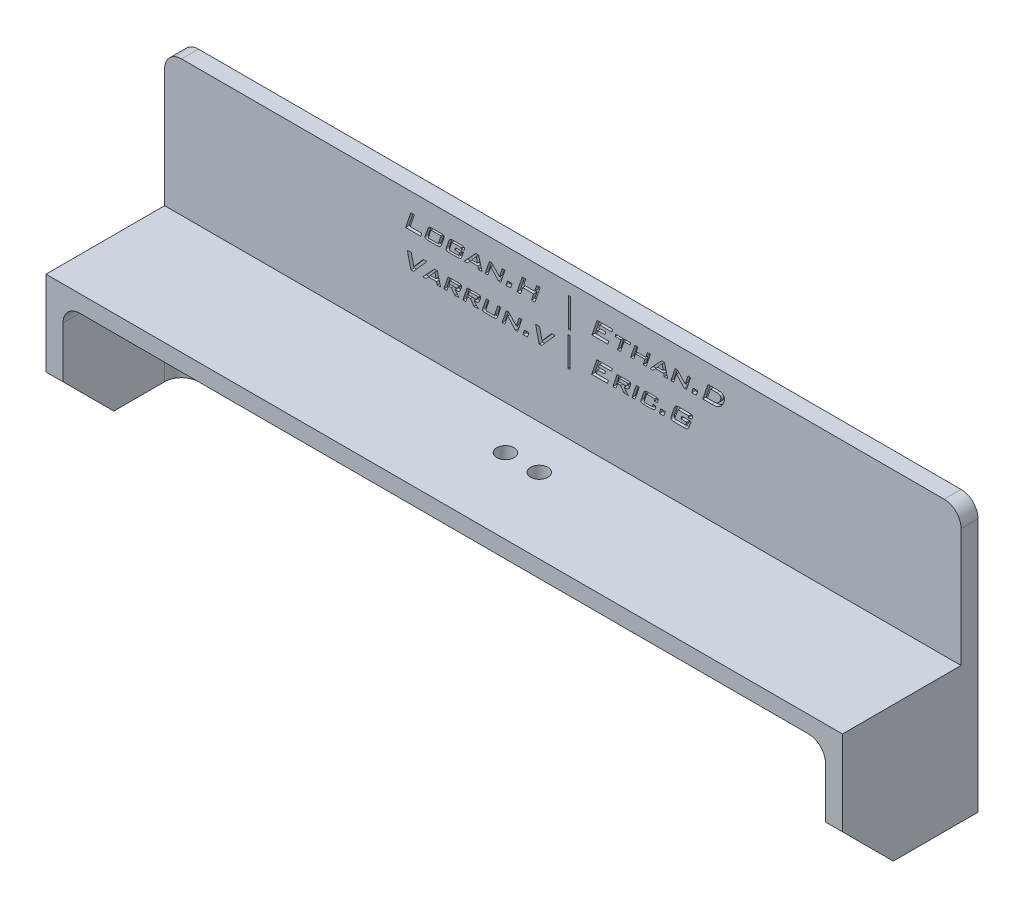
SolidWorks part; units mm, degrees
material "ABS PC"
ref_plane "Front Plane" through (0, 0, 0) normal (0, 0, 1) x (1, 0, 0)
ref_plane "Top Plane" through (0, 0, 0) normal (0, 1, 0) x (1, 0, 0)
ref_plane "Right Plane" through (0, 0, 0) normal (1, 0, 0) x (0, 0, -1)
sketch "Sketch1" plane through (0, 0, 0) normal (0, 1, 0) x (1, 0, 0)
  line L1 (0, 0) -> (235, 0)
  line L2 (0, 0) -> (0, -40)
  line L3 (0, -40) -> (235, -40)
  line L4 (235, 0) -> (235, -40)
  dimension "D1" = 40
  dimension "D2" = 235
extrude "Boss-Extrude1" add sketch "Sketch1" along normal blind 5
sketch "Sketch2" plane through (0, 0, 0) normal (0, -1, 0) x (1, 0, 0)
  line L0 (0, 0) -> (0, 40) construction
  line L1 (5, 5) -> (230, 5)
  line L2 (0, 5) -> (0, 0)
  line L3 (0, 0) -> (235, 0)
  line L4 (235, 5) -> (235, 0)
  line L6 (235, 40) -> (230, 40)
  line L7 (235, 40) -> (235, 5)
  line L9 (230, 40) -> (230, 5)
  line L10 (0, 40) -> (5, 40)
  line L11 (0, 40) -> (0, 5)
  line L13 (5, 40) -> (5, 5)
  dimension "D1" = 5
extrude "Boss-Extrude2" add sketch "Sketch2" along normal blind 35
sketch "Sketch3" plane through (0, 0, 5) normal (0, 0, 1) x (1, 0, 0)
  line L0 (0, -15) -> (230, -15) construction
  line L1 (0, -35) -> (0, 0) construction
  line L2 (230, -35) -> (230, 0) construction
  line L3 (230, -35) -> (5, -35) construction
  line L4 (117.5, -35) -> (117.5, 0) construction
  line L5 (5, 0) -> (230, 0) construction
  point P12 (55, -15)
  point P13 (180, -15)
  point P14 (117.5, -15)
  dimension "D1" = 20
  dimension "D2" = 125
hole_wizard "M4 Clearance Hole1" positions "Sketch3" profile "Sketch4" hole size "M4" standard "ANSI Metric" end condition through all
sketch "Sketch4" plane through (117.5, -15, 5) normal (1, 0, 0) x (0, -1, 0)
  line L0 (0, 0) -> (0, 5)
  line L1 (0, 5) -> (2.25, 5)
  line L2 (2.25, 5) -> (2.25, 0)
  line L5 (2.25, 0) -> (0, 0)
  line L11 (0, -6.35) -> (0, 107.95) construction
  dimension "Thru Hole Dia." = 4.5
  dimension "Thru Hole Depth" = 5
sketch "Sketch5" plane through (0, 0, 0) normal (0, -1, 0) x (1, 0, 0)
  line L0 (0, 17.85) -> (230, 17.85) construction
  line L1 (0, 5) -> (0, 40) construction
  line L2 (230, 40) -> (230, 5) construction
  line L3 (5, 40) -> (230, 40) construction
  line L4 (117.5, 40) -> (117.5, 5) construction
  line L5 (230, 5) -> (5, 5) construction
  line L7 (235, 0) -> (0, 0) construction
  point P17 (123.391, 17.85)
  point P19 (113.391, 17.85)
  dimension "D1" = 17.85
  dimension "D2" = 10
  dimension "D3" = 4.109
hole_wizard "Ø5.1 (5.1) Diameter Hole1" positions "Sketch5" profile "Sketch6" hole size "Ø5.1" standard "ANSI Metric" end condition through all
sketch "Sketch6" plane through (113.391, 0, 17.85) normal (1, 0, 0) x (0, 0, -1)
  line L0 (0, 0) -> (0, 5)
  line L1 (0, 5) -> (2.55, 5)
  line L2 (2.55, 5) -> (2.55, 0)
  line L5 (2.55, 0) -> (0, 0)
  line L11 (0, -6.35) -> (0, 107.95) construction
  dimension "Thru Hole Dia." = 5.1
  dimension "Thru Hole Depth" = 5
sketch "Sketch7" plane through (0, 5, 0) normal (0, 1, 0) x (1, 0, 0)
  line L5 (235, -40) -> (235, 0) construction
  line L6 (0, 0) -> (235, 0)
  line L7 (0, 0) -> (0, -5)
  line L8 (0, -5) -> (235, -5)
  line L9 (235, 0) -> (235, -5)
  dimension "D2" = 5
extrude "Boss-Extrude3" add sketch "Sketch7" along normal blind 40
fillet "Fillet1" radius 5 2 edges at (235, 45, 2.5) (0, 45, 2.5)
fillet "Fillet2" radius 5 5 edges at (230, -17.5, 5) (230, 0, 22.5) (117.5, 0, 5) (5, -17.5, 5) (5, 0, 22.5)
chamfer "Chamfer3" distance 15 angle 45 2 edges at (232.5, -35, 40) (2.5, -35, 40)
sketch "Sketch9" plane through (0, 0, 5) normal (0, 0, 1) x (1, 0, 0)
  line L0 (70, 45) -> (70, 5) construction
  line L1 (5, 45) -> (230, 45) construction
  line L2 (0, 5) -> (235, 5) construction
  line L3 (70, 35) -> (235, 35) construction
  line L4 (235, 40) -> (235, 5) construction
  line L5 (0, 40) -> (0, 5) construction
  text T0 "<i>Logan.H  </i>| <i>Ethan.D</i>\r\n<i>Varrun.V </i>| <i>Eric.G</i>\r\n" font "BankGothic Md BT" height 4.5
  dimension "D1" = 10
  dimension "D2" = 70
extrude "Cut-Extrude1" cut sketch "Sketch9" against normal blind 1
